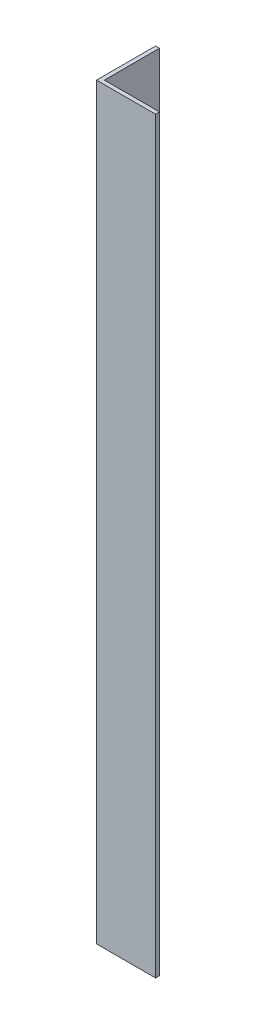
SolidWorks part; units mm, degrees
material "1060 Сплав"
ref_plane "Спереди" through (0, 0, 0) normal (0, 0, 1) x (1, 0, 0)
ref_plane "Сверху" through (0, 0, 0) normal (0, 1, 0) x (1, 0, 0)
ref_plane "Справа" through (0, 0, 0) normal (1, 0, 0) x (0, 0, -1)
sketch "Эскиз1" plane through (0, 0, 0) normal (0, 1, 0) x (1, 0, 0)
  line L0 (0, 0) -> (0, 15)
  line L1 (0, 15) -> (1, 15)
  line L2 (1, 15) -> (1, 1)
  line L3 (1, 1) -> (15, 1)
  line L4 (15, 1) -> (15, 0)
  line L5 (15, 0) -> (0, 0)
  dimension "D1" = 1
  dimension "D2" = 15
extrude "Бобышка-Вытянуть1" add sketch "Эскиз1" along normal blind 190
